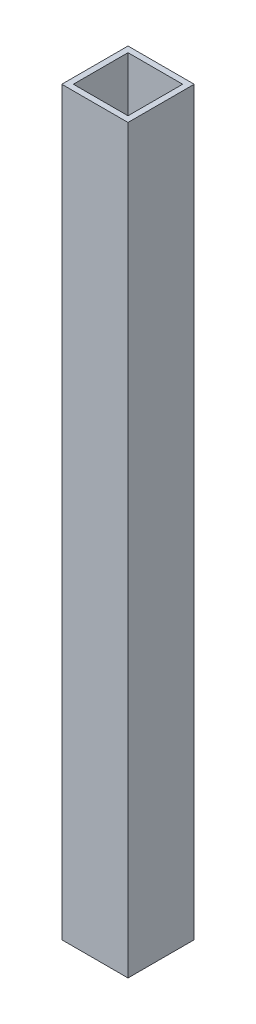
SolidWorks part; units mm, degrees
ref_plane "Front Plane" through (0, 0, 0) normal (0, 0, 1) x (1, 0, 0)
ref_plane "Top Plane" through (0, 0, 0) normal (0, 1, 0) x (1, 0, 0)
ref_plane "Right Plane" through (0, 0, 0) normal (1, 0, 0) x (0, 0, -1)
sketch "Sketch1" plane through (0, 0, 0) normal (0, 1, 0) x (1, 0, 0)
  line L1 (-7.8, -7.8) -> (7.8, -7.8)
  line L2 (-7.8, -7.8) -> (-7.8, 7.8)
  line L3 (-7.8, 7.8) -> (7.8, 7.8)
  line L4 (7.8, -7.8) -> (7.8, 7.8)
  line L5 (-7.8, -7.8) -> (7.8, 7.8) construction
  line L6 (-7.8, 7.8) -> (7.8, -7.8) construction
  line L7 (-9.45, -9.45) -> (9.45, -9.45)
  line L8 (-9.45, -9.45) -> (-9.45, 9.45)
  line L9 (-9.45, 9.45) -> (9.45, 9.45)
  line L10 (9.45, -9.45) -> (9.45, 9.45)
  point P0 (0, 0)
  dimension "D1" = 15.6
  dimension "D2" = 15.6
  dimension "D3" = 18.9
  dimension "D4" = 18.9
  dimension "D5" = 9.45
  dimension "D6" = 9.45
extrude "Boss-Extrude1" add sketch "Sketch1" along normal blind 211.5
